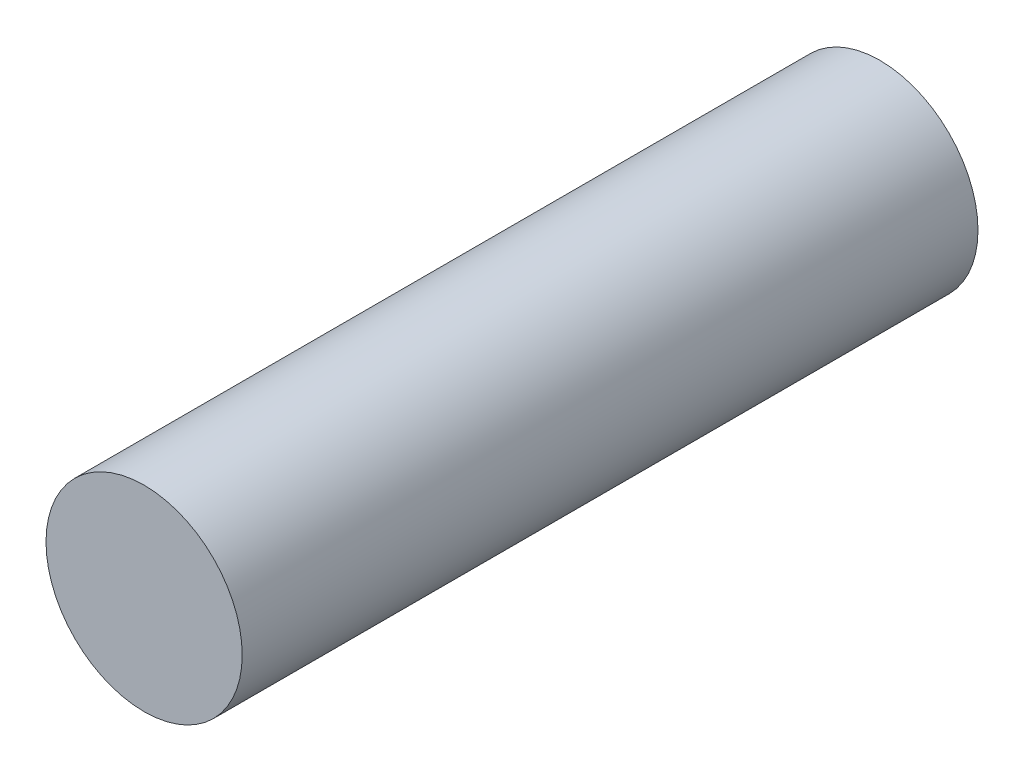
SolidWorks part; units mm, degrees
ref_plane "Plan de face" through (0, 0, 0) normal (0, 0, 1) x (1, 0, 0)
ref_plane "Plan de dessus" through (0, 0, 0) normal (0, 1, 0) x (1, 0, 0)
ref_plane "Plan de droite" through (0, 0, 0) normal (1, 0, 0) x (0, 0, -1)
sketch "Esquisse1" plane through (0, 0, 0) normal (0, 0, 1) x (1, 0, 0)
  circle A0 centre (0, 0) radius 4
extrude "Boss.-Extru.1" add sketch "Esquisse1" along normal blind 30
